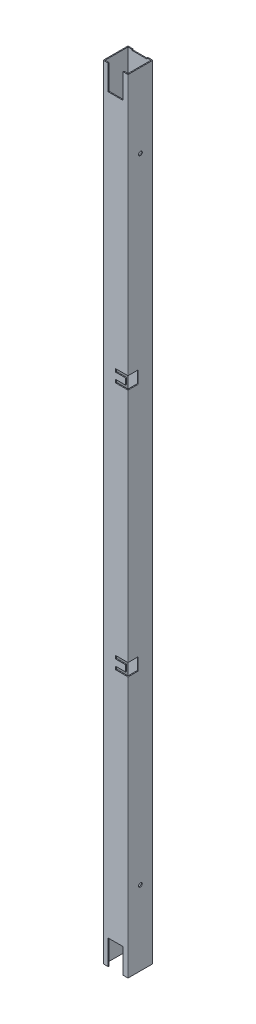
SolidWorks part; units mm, degrees
ref_plane "Front Plane" through (0, 0, 0) normal (0, 0, 1) x (1, 0, 0)
ref_plane "Top Plane" through (0, 0, 0) normal (0, 1, 0) x (1, 0, 0)
ref_plane "Right Plane" through (0, 0, 0) normal (1, 0, 0) x (0, 0, -1)
sketch "Sketch1" plane through (0, 0, 0) normal (0, 1, 0) x (1, 0, 0)
  line L0 (1.5, 1.5) -> (38.5, 1.5)
  line L1 (0.5, 0) -> (39.5, 0)
  line L2 (0, 0.5) -> (0, 39.5)
  line L3 (0.5, 40) -> (39.5, 40)
  line L4 (40, 0.5) -> (40, 39.5)
  line L5 (38.5, 1.5) -> (38.5, 38.5)
  line L6 (1.5, 38.5) -> (38.5, 38.5)
  line L7 (1.5, 1.5) -> (1.5, 38.5)
  arc A0 (39.5, 0) -> (40, 0.5) centre (39.5, 0.5) ccw
  arc A1 (0.5, 0) -> (0, 0.5) centre (0.5, 0.5) cw
  arc A2 (0, 39.5) -> (0.5, 40) centre (0.5, 39.5) cw
  arc A3 (39.5, 40) -> (40, 39.5) centre (39.5, 39.5) cw
  arc A4 (38.5, 1.5) -> (38.5, 1.5) centre (38.5, 1.5) ccw
  arc A5 (38.5, 38.5) -> (38.5, 38.5) centre (38.5, 38.5) cw
  arc A6 (1.5, 38.5) -> (1.5, 38.5) centre (1.5, 38.5) cw
  arc A7 (1.5, 1.5) -> (1.5, 1.5) centre (1.5, 1.5) cw
  point P9 (0, 0)
  dimension "D3" = 0.5
  dimension "D1" = 40
  dimension "D2" = 40
  dimension "D4" = 1.5
extrude "Boss-Extrude1" add sketch "Sketch1" along normal blind 1260
sketch "Sketch2" plane through (0, 0, 0) normal (0, 0, 1) x (1, 0, 0)
  line L0 (0.5, 1260) -> (39.5, 1260) construction
  line L1 (32, 1260) -> (8.1, 1260)
  line L2 (32, 1260) -> (32, 1220)
  line L3 (32, 1220) -> (8.1, 1220)
  line L4 (8.1, 1260) -> (8.1, 1220)
  line L5 (40, 1260) -> (40, 0) construction
  line L6 (0, 1260) -> (0, 0) construction
  dimension "D1" = 40
  dimension "D2" = 8
  dimension "D3" = 8.1
extrude "Cut-Extrude1" cut sketch "Sketch2" against normal blind 20
sketch "Sketch3" plane through (0, 0, -38.5) normal (0, 0, 1) x (1, 0, 0)
  line L0 (32, 1220) -> (32, 1260) construction
  line L1 (8.1, 1260) -> (32, 1260)
  line L2 (8.1, 1260) -> (8.1, 1258.4)
  line L3 (8.1, 1258.4) -> (32, 1258.4)
  line L4 (32, 1260) -> (32, 1258.4)
  line L5 (8.1, 1260) -> (8.1, 1220) construction
  line L6 (32, 1220) -> (8.1, 1220)
  line L7 (32, 1220) -> (32, 1221.6)
  line L8 (32, 1221.6) -> (8.1, 1221.6)
  line L9 (8.1, 1220) -> (8.1, 1221.6)
  dimension "D1" = 1.6
  dimension "D2" = 1.6
extrude "Cut-Extrude2" cut sketch "Sketch3" against normal blind 20
ref_plane "Plane1" through (0, 630, 0) normal (0, 1, 0) x (1, 0, 0)
mirror "Mirror1" about plane through (0, 630, 0) normal (0, 1, 0) of "Cut-Extrude2", "Cut-Extrude1"
sketch "Sketch4" plane through (40, 0, 0) normal (1, 0, 0) x (0, 0, -1)
  line L10 (0, 840) -> (16.5, 840)
  line L11 (0, 1260) -> (0, 0) construction
  line L12 (16.5, 840) -> (16.5, 820)
  line L13 (16.5, 820) -> (0, 820)
  line L14 (0, 820) -> (0, 825)
  line L15 (0, 825) -> (5, 825)
  line L16 (5, 825) -> (5, 835)
  line L17 (5, 835) -> (0, 835)
  line L18 (0, 835) -> (0, 840)
  line L19 (0.5, 1260) -> (39.5, 1260) construction
  point P9 (0, 837.5)
  point P11 (16.5, 830)
  point P12 (5, 830)
  dimension "D1" = 16.5
  dimension "D2" = 5
  dimension "D3" = 10
  dimension "D4" = 20
  dimension "D5" = 420
extrude "Cut-Extrude3" cut sketch "Sketch4" against normal blind 20
sketch "Sketch5" plane through (0, 0, 0) normal (0, 0, 1) x (1, 0, 0)
  line L0 (20, 835) -> (39.5, 835) construction
  line L1 (36, 835) -> (40, 835)
  line L2 (36, 835) -> (36, 825)
  line L3 (36, 825) -> (40, 825)
  line L4 (40, 835) -> (40, 825)
  line L5 (40, 835) -> (40, 825) construction
  line L6 (40, 820) -> (40, 840) construction
  line L7 (20, 825) -> (39.5, 825) construction
  dimension "D1" = 4
extrude "Cut-Extrude4" cut sketch "Sketch5" against normal blind 10
pattern_linear "LPattern1" count 2 spacing 400 along (0, -1, 0) of "Cut-Extrude3", "Cut-Extrude4"
sketch "Sketch6" plane through (40, 0, 0) normal (1, 0, 0) x (0, 0, -1)
  line L0 (40, 1260) -> (40, 0) construction
  line L1 (0.5, 1260) -> (39.5, 1260) construction
  line L2 (40, 630) -> (0.5, 630) construction
  line L3 (0.5, 820) -> (0.5, 440) construction
  circle A0 centre (20, 1140) radius 3
  circle A1 centre (20, 120) radius 3
  dimension "D1" = 6
  dimension "D3" = 120
  dimension "D2" = 20
extrude "Cut-Extrude5" cut sketch "Sketch6" against normal through all
